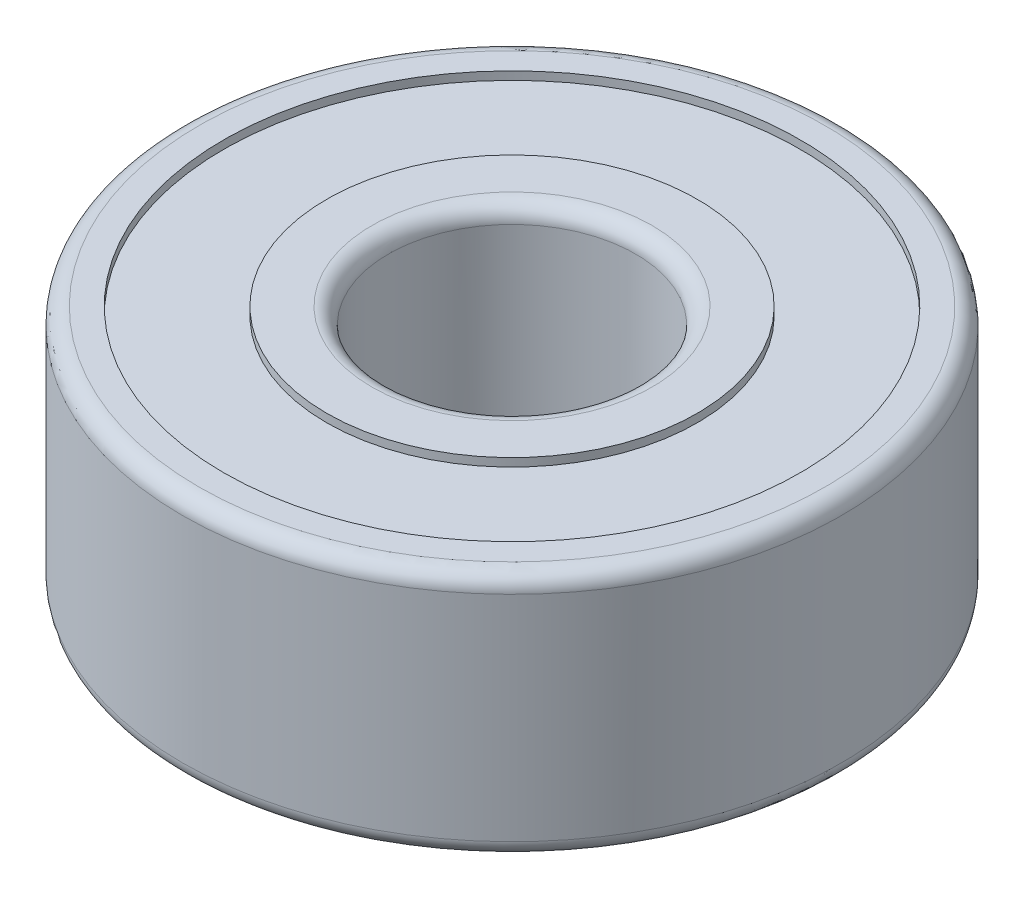
SolidWorks part; units mm, degrees
material "Plain Carbon Steel"
ref_plane "Front Plane" through (0, 0, 0) normal (0, 0, 1) x (1, 0, 0)
ref_plane "Top Plane" through (0, 0, 0) normal (0, 1, 0) x (1, 0, 0)
ref_plane "Right Plane" through (0, 0, 0) normal (1, 0, 0) x (0, 0, -1)
sketch "Sketch1" plane through (0, 0, 0) normal (1, 0, 0) x (0, 0, -1)
  line L0 (-4, 1.5) -> (-3.5, 1.5)
  line L1 (-3.5, 1.5) -> (-3.5, 1.4)
  line L2 (-3.5, 1.4) -> (-2.25, 1.4)
  line L3 (-2.25, 1.4) -> (-2.25, 1.5)
  line L4 (-2.25, 1.5) -> (-1.5, 1.5)
  line L5 (-1.5, 1.5) -> (-1.5, 0)
  line L6 (-1.5, 0) -> (-4, 0)
  line L7 (-4, 0) -> (-4, 1.5)
  line L8 (0, 17.3077) -> (0, -10.2308) construction
  point P11 (-2.75, 0)
  dimension "D1" = 3
  dimension "D2" = 8
  dimension "D3" = 1.5
  dimension "D4" = 0.75
  dimension "D5" = 0.5
  dimension "D6" = 0.1
revolve "Revolve1" add sketch "Sketch1" angle 360 about L8
fillet "Fillet1" radius 0.2 2 edges at (0, 1.5, 1.5) (0, 1.5, 4)
mirror "Mirror1" about plane through (0, 0, 0) normal (0, 1, 0) of "Fillet1", "Revolve1"
